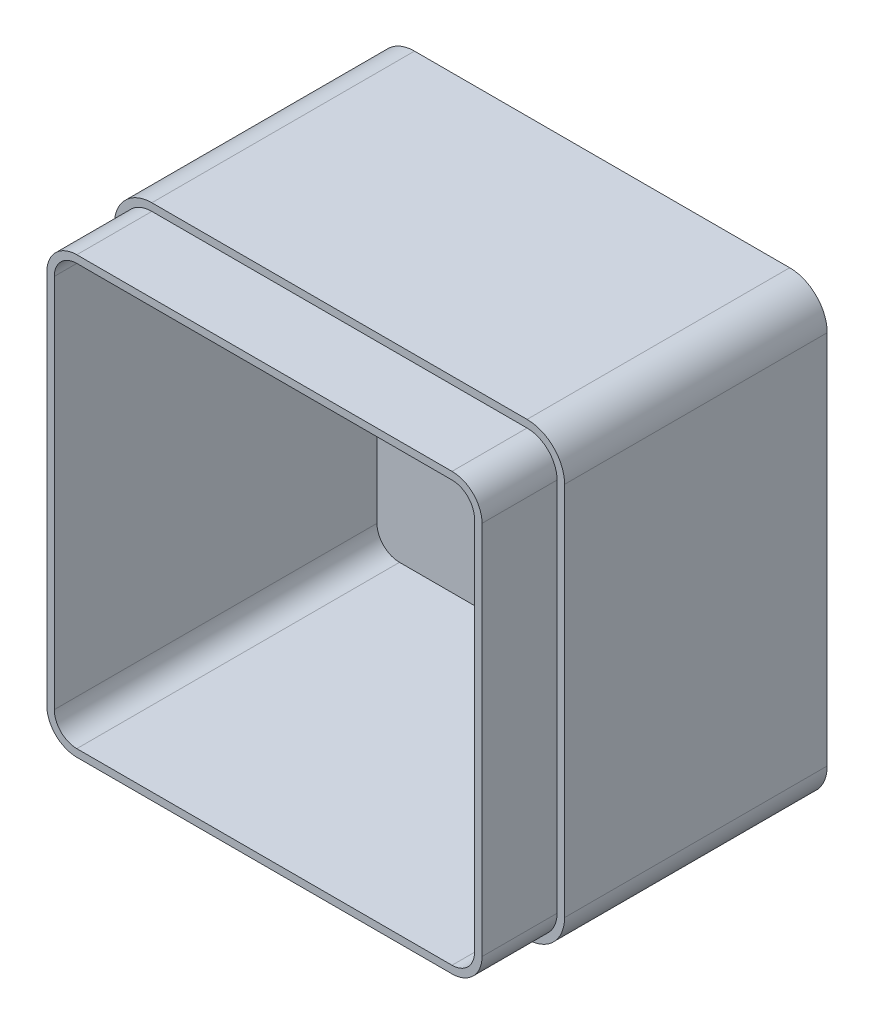
SolidWorks part; units mm, degrees
ref_plane "Front Plane" through (0, 0, 0) normal (0, 0, 1) x (1, 0, 0)
ref_plane "Top Plane" through (0, 0, 0) normal (0, 1, 0) x (1, 0, 0)
ref_plane "Right Plane" through (0, 0, 0) normal (1, 0, 0) x (0, 0, -1)
sketch "Sketch1" plane through (0, 0, 0) normal (0, 0, 1) x (1, 0, 0)
  line L1 (0, 0) -> (1200, 0)
  line L2 (0, 0) -> (0, 1200)
  line L3 (0, 1200) -> (1200, 1200)
  line L4 (1200, 0) -> (1200, 1200)
  dimension "D1" = 1200
  dimension "D2" = 1200
extrude "Boss-Extrude1" add sketch "Sketch1" along normal blind 900
fillet "Fillet1" radius 100 4 edges at (1200, 0, 450) (0, 0, 450) (1200, 1200, 450) (0, 1200, 450)
shell "Shell1" thickness 40
sketch "Sketch4" plane through (0, 0, 900) normal (0, 0, 1) x (1, 0, 0)
  line L4 (100, 0) -> (1100, 0)
  line L5 (1200, 100) -> (1200, 1100)
  line L6 (1100, 1200) -> (100, 1200)
  line L7 (0, 1100) -> (0, 100)
  line L8 (100, 0) -> (1100, 0)
  line L9 (1200, 100) -> (1200, 1100)
  line L10 (1100, 1200) -> (100, 1200)
  line L11 (0, 1100) -> (0, 100)
  line L16 (100, 20) -> (1100, 20)
  line L17 (1180, 100) -> (1180, 1100)
  line L18 (1100, 1180) -> (100, 1180)
  line L19 (20, 1100) -> (20, 100)
  line L20 (100, 20) -> (1100, 20)
  line L21 (1180, 100) -> (1180, 1100)
  line L22 (1100, 1180) -> (100, 1180)
  line L23 (20, 1100) -> (20, 100)
  arc A4 (1100, 0) -> (1200, 100) centre (1100, 100) ccw
  arc A5 (1200, 1100) -> (1100, 1200) centre (1100, 1100) ccw
  arc A6 (100, 1200) -> (0, 1100) centre (100, 1100) ccw
  arc A7 (0, 100) -> (100, 0) centre (100, 100) ccw
  arc A8 (1100, 0) -> (1200, 100) centre (1100, 100) ccw
  arc A9 (1200, 1100) -> (1100, 1200) centre (1100, 1100) ccw
  arc A10 (100, 1200) -> (0, 1100) centre (100, 1100) ccw
  arc A11 (0, 100) -> (100, 0) centre (100, 100) ccw
  arc A16 (1100, 20) -> (1180, 100) centre (1100, 100) ccw
  arc A17 (1180, 1100) -> (1100, 1180) centre (1100, 1100) ccw
  arc A18 (100, 1180) -> (20, 1100) centre (100, 1100) ccw
  arc A19 (20, 100) -> (100, 20) centre (100, 100) ccw
  arc A20 (1100, 20) -> (1180, 100) centre (1100, 100) ccw
  arc A21 (1180, 1100) -> (1100, 1180) centre (1100, 1100) ccw
  arc A22 (100, 1180) -> (20, 1100) centre (100, 1100) ccw
  arc A23 (20, 100) -> (100, 20) centre (100, 100) ccw
  dimension "D1" = 0
  dimension "D2" = 20
extrude "Cut-Extrude2" cut sketch "Sketch4" against normal blind 200
scale "Scale3" scale about origin uniform scaling yes scale factor 0.1
